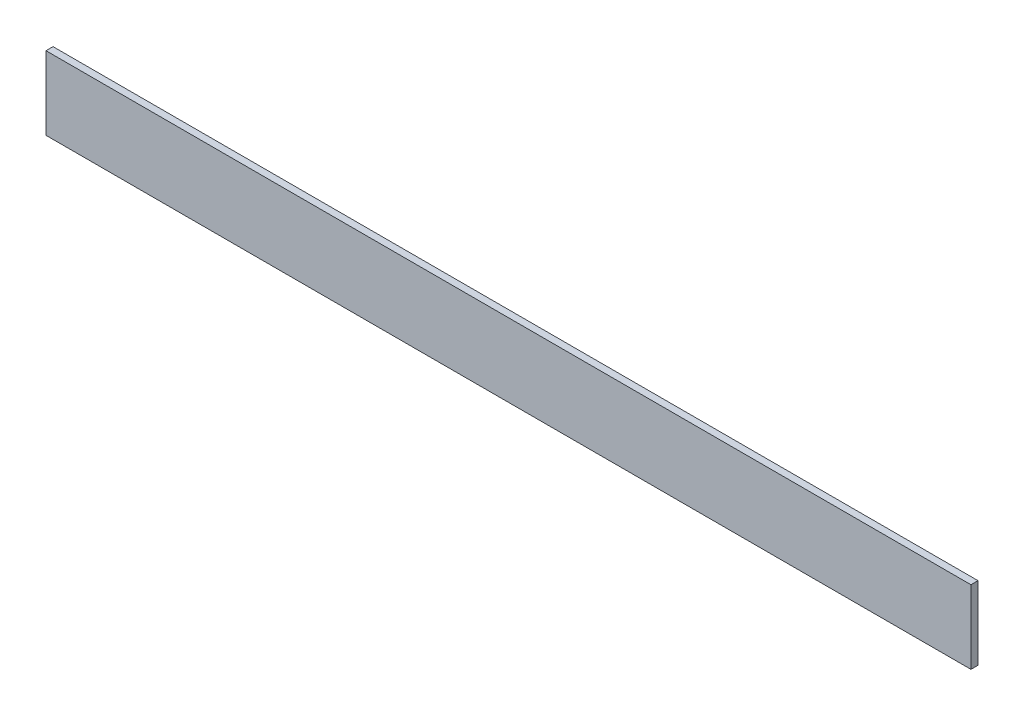
SolidWorks part; units mm, degrees
ref_plane "Front Plane" through (0, 0, 0) normal (0, 0, 1) x (1, 0, 0)
ref_plane "Top Plane" through (0, 0, 0) normal (0, 1, 0) x (1, 0, 0)
ref_plane "Right Plane" through (0, 0, 0) normal (1, 0, 0) x (0, 0, -1)
sketch "Sketch1" plane through (0, 0, 0) normal (0, 0, 1) x (1, 0, 0)
  line L0 (198.0279, 5.7353) -> (194.8529, 5.7353) construction
  line L1 (-221.2271, 38.7138) -> (194.8529, 38.7138)
  line L2 (-221.2271, 38.7138) -> (-221.2271, 5.7353)
  line L3 (-221.2271, 5.7353) -> (194.8529, 5.7353)
  line L4 (194.8529, 38.7138) -> (194.8529, 5.7353)
extrude "Boss-Extrude1" add sketch "Sketch1" along normal blind 3.175
